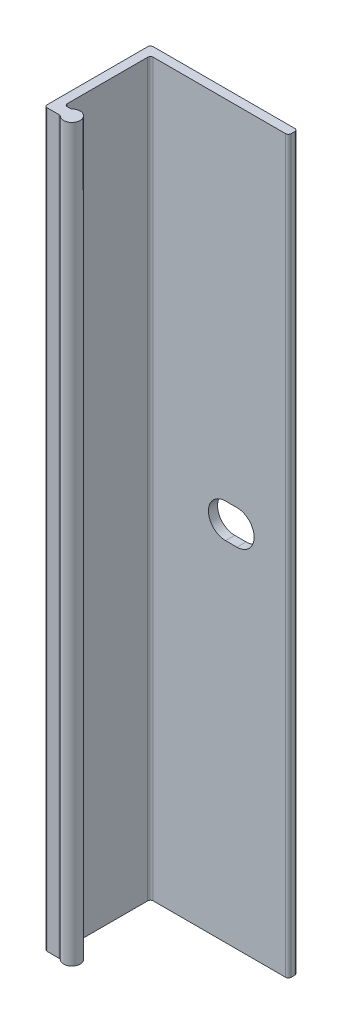
SolidWorks part; units mm, degrees
material "6463-T6"
ref_plane "Front Plane" through (0, 0, 0) normal (0, 0, 1) x (1, 0, 0)
ref_plane "Top Plane" through (0, 0, 0) normal (0, 1, 0) x (1, 0, 0)
ref_plane "Right Plane" through (0, 0, 0) normal (1, 0, 0) x (0, 0, -1)
sketch "Sketch2" plane through (0, 0, 0) normal (0, 1, 0) x (1, 0, 0)
  line L0 (0, -55) -> (0, 55) construction
  line L16 (0.381, 0) -> (20.066, 0)
  line L18 (20.447, -0.381) -> (20.447, -0.889)
  line L19 (20.066, -1.27) -> (1.651, -1.27)
  line L20 (1.27, -1.651) -> (1.27, -12.827)
  line L52 (0, -0.381) -> (0, -14.351)
  line L55 (0.381, -14.732) -> (2.04, -14.732)
  line L56 (1.651, -13.208) -> (2.04, -13.208)
  arc A11 (20.066, 0) -> (20.447, -0.381) centre (20.066, -0.381) cw
  arc A12 (20.447, -0.889) -> (20.066, -1.27) centre (20.066, -0.889) cw
  arc A19 (1.651, -1.27) -> (1.27, -1.651) centre (1.651, -1.651) ccw
  arc A21 (2.292, -14.8272) -> (2.292, -13.1128) centre (3.048, -13.97) ccw
  arc A22 (1.27, -12.827) -> (1.651, -13.208) centre (1.651, -12.827) ccw
  arc A24 (2.04, -14.732) -> (2.292, -14.8272) centre (2.04, -15.113) cw
  arc A25 (2.292, -13.1128) -> (2.04, -13.208) centre (2.04, -12.827) cw
  arc A26 (0.381, -14.732) -> (0, -14.351) centre (0.381, -14.351) cw
  arc A27 (0.381, 0) -> (0, -0.381) centre (0.381, -0.381) ccw
  point P7 (0, -14.732)
  point P16 (20.447, 0)
  point P19 (20.447, -1.27)
  point P22 (1.27, -1.27)
  point P30 (1.27, -13.208)
  point P36 (2.1961, -14.732)
  point P39 (2.1961, -13.208)
  point P43 (0, -8.89)
  dimension "D1" = 20.447
  dimension "D7" = 0.381
  dimension "D6" = 13.97
  dimension "D10" = 0.389
  dimension "D11" = 14.732
  dimension "D9" = 1.143
  dimension "D4" = 0.381
  dimension "D2" = 1.27
  dimension "D3" = 1.27
  dimension "D5" = 5.842
  dimension "D8" = 3.048
extrude "Boss-Extrude1" add sketch "Sketch2" along normal mid plane 101.6
sketch "Sketch7" plane through (0, 0, 1.27) normal (0, 0, 1) x (1, 0, 0)
  line L0 (11.7158, 0) -> (13.3033, 0) construction
  line L1 (11.7158, 2.3812) -> (13.3033, 2.3813)
  line L2 (11.7158, -2.3813) -> (13.3033, -2.3813)
  line L3 (0, 0) -> (20.447, 0) construction
  line L4 (20.447, 50.8) -> (20.447, -50.8) construction
  arc A0 (11.7158, 2.3812) -> (11.7158, -2.3813) centre (11.7158, 0) ccw
  arc A1 (13.3033, -2.3813) -> (13.3033, 2.3813) centre (13.3033, 0) ccw
  point P3 (12.5095, 0)
  dimension "D1" = 4.7625
  dimension "D2" = 6.35
  dimension "D3" = 7.9375
extrude "Cut-Extrude1" cut sketch "Sketch7" against normal through all
